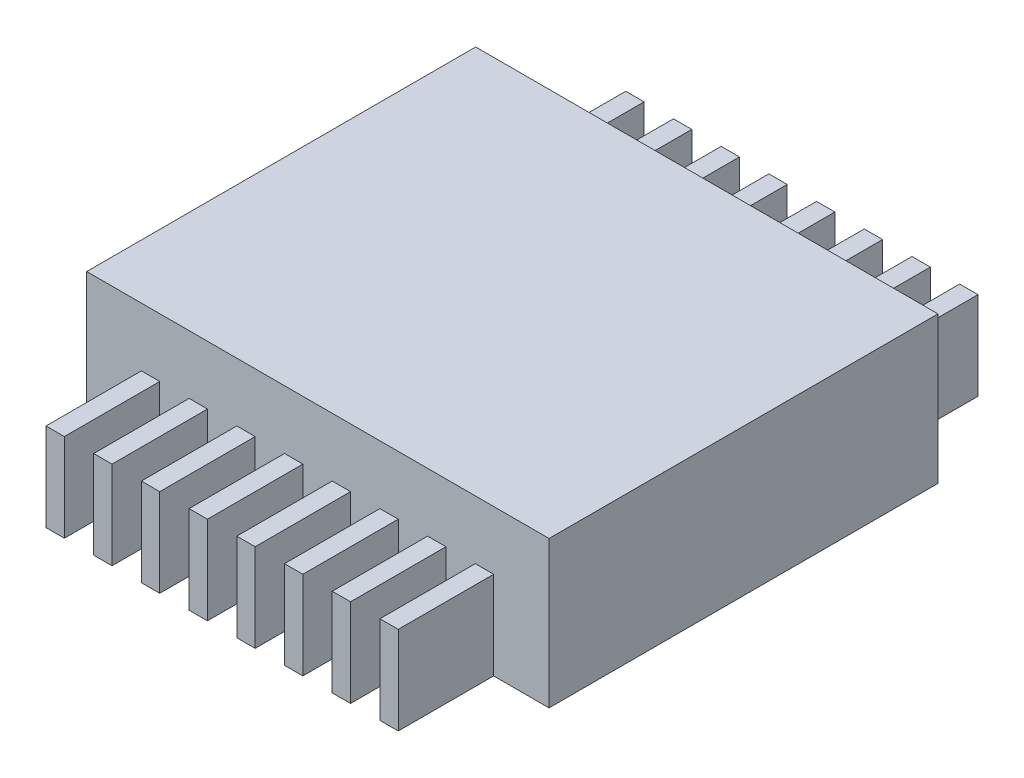
SolidWorks part; units mm, degrees
ref_plane "Front Plane" through (0, 0, 0) normal (0, 0, 1) x (1, 0, 0)
ref_plane "Top Plane" through (0, 0, 0) normal (0, 1, 0) x (1, 0, 0)
ref_plane "Right Plane" through (0, 0, 0) normal (1, 0, 0) x (0, 0, -1)
sketch "Sketch1" plane through (0, 0, 0) normal (0, 1, 0) x (1, 0, 0)
  line L0 (0, -2.65) -> (0, 46.2078) construction
  line L1 (-3.15, 2.65) -> (3.15, 2.65)
  line L2 (-3.15, 2.65) -> (-3.15, -2.65)
  line L3 (-3.15, -2.65) -> (3.15, -2.65)
  line L4 (3.15, 2.65) -> (3.15, -2.65)
  line L5 (-3.15, 0) -> (69.3772, 0) construction
  dimension "D1" = 5.3
  dimension "D2" = 6.3
extrude "Boss-Extrude1" add sketch "Sketch1" along normal blind 2
sketch "Sketch2" plane through (0, 0, 2.65) normal (0, 0, 1) x (1, 0, 0)
  line L0 (-3.15, 0) -> (3.15, 0) construction
  line L1 (-2.405, 0) -> (-2.155, 0)
  line L2 (-2.405, 0) -> (-2.405, 1.2)
  line L3 (-2.405, 1.2) -> (-2.155, 1.2)
  line L4 (-2.155, 0) -> (-2.155, 1.2)
  line L5 (-2.28, 1.2) -> (-2.28, -0.8397) construction
  point P6 (0, 0)
  point P9 (0, 0)
  dimension "D1" = 2.28
  dimension "D2" = 0.25
  dimension "D3" = 1.2
extrude "Boss-Extrude2" add sketch "Sketch2" along normal blind 1.3
pattern_linear "LPattern1" count 8 spacing 0.65 along (1, 0, 0) of "Boss-Extrude2"
mirror "Mirror1" about plane through (0, 0, 0) normal (0, 0, 1) of "LPattern1", "Boss-Extrude2"
